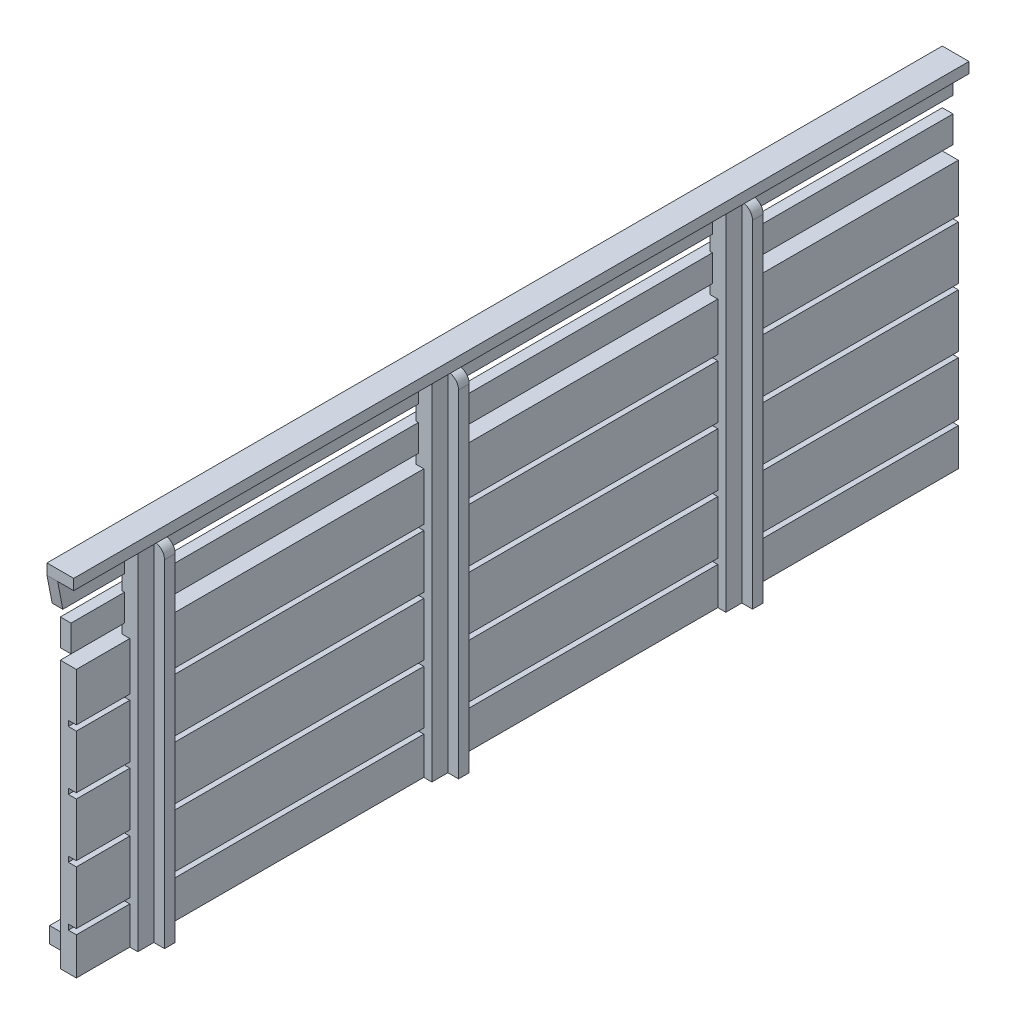
SolidWorks part; units mm, degrees
ref_plane "Front Plane" through (0, 0, 0) normal (0, 0, 1) x (1, 0, 0)
ref_plane "Top Plane" through (0, 0, 0) normal (0, 1, 0) x (1, 0, 0)
ref_plane "Right Plane" through (0, 0, 0) normal (1, 0, 0) x (0, 0, -1)
sketch "Sketch1" plane through (0, 0, 0) normal (1, 0, 0) x (0, 0, -1)
  line L1 (-82.5, 25) -> (82.5, 25)
  line L2 (-82.5, 25) -> (-82.5, -25)
  line L3 (-82.5, -25) -> (82.5, -25)
  line L4 (82.5, 25) -> (82.5, -25)
  line L5 (-82.5, 25) -> (82.5, -25) construction
  line L6 (-82.5, -25) -> (82.5, 25) construction
  point P0 (0, 0)
  dimension "D1" = 165
  dimension "D2" = 50
extrude "Boss-Extrude1" add sketch "Sketch1" along normal blind 3
sketch "Sketch2" plane through (3, 0, 0) normal (1, 0, 0) x (0, 0, -1)
  line L0 (-82.5, 25) -> (-82.5, -25) construction
  line L1 (-82.5, -17) -> (82.5, -17)
  line L2 (-82.5, -17) -> (-82.5, -18)
  line L3 (-82.5, -18) -> (82.5, -18)
  line L4 (82.5, -17) -> (82.5, -18)
  line L5 (82.5, -25) -> (82.5, 25) construction
  line L6 (-82.5, -25) -> (82.5, -25) construction
  line L7 (82.5, 25) -> (-82.5, 25) construction
  line L8 (-82.5, -6) -> (82.5, -6)
  line L9 (-82.5, -6) -> (-82.5, -7)
  line L10 (-82.5, -7) -> (82.5, -7)
  line L11 (82.5, -6) -> (82.5, -7)
  line L12 (-82.5, 5) -> (82.5, 5)
  line L13 (-82.5, 5) -> (-82.5, 4)
  line L14 (-82.5, 4) -> (82.5, 4)
  line L15 (82.5, 5) -> (82.5, 4)
  line L16 (-82.5, 16) -> (82.5, 16)
  line L17 (-82.5, 16) -> (-82.5, 15)
  line L18 (-82.5, 15) -> (82.5, 15)
  line L19 (82.5, 16) -> (82.5, 15)
  dimension "D1" = 1
  dimension "D2" = 7
  dimension "D3" = 1
  dimension "D4" = 10
  dimension "D5" = 1
  dimension "D6" = 10
  dimension "D7" = 1
  dimension "D8" = 10
  dimension "D9" = 9
extrude "Cut-Extrude1" cut sketch "Sketch2" against normal blind 1.5
sketch "Sketch3" plane through (3, 0, 0) normal (1, 0, 0) x (0, 0, -1)
  line L6 (-67.5, -25) -> (-72.5, -25)
  line L7 (-82.5, -25) -> (82.5, -25) construction
  line L8 (42.5, -25) -> (37.5, -25)
  line L9 (42.5, -25) -> (42.5, 40)
  line L10 (42.5, 40) -> (37.5, 40)
  line L11 (37.5, -25) -> (37.5, 40)
  line L12 (82.5, -25) -> (82.5, -18) construction
  line L13 (-67.5, -25) -> (-67.5, 40)
  line L14 (-12.5, -25) -> (-17.5, -25)
  line L15 (-12.5, -25) -> (-12.5, 40)
  line L16 (-12.5, 40) -> (-17.5, 40)
  line L17 (-17.5, -25) -> (-17.5, 40)
  line L22 (-67.5, 40) -> (-72.5, 40)
  line L23 (-72.5, -25) -> (-72.5, 40)
  dimension "D1" = 65
  dimension "D2" = 40
  dimension "D3" = 5
  dimension "D4" = 5
  dimension "D5" = 65
  dimension "D6" = 50
  dimension "D7" = 5
  dimension "D8" = 50
  dimension "D9" = 65
extrude "Boss-Extrude2" add sketch "Sketch3" along normal mid plane 3
sketch "Sketch4" plane through (4.5, 0, 0) normal (1, 0, 0) x (0, 0, -1)
  line L0 (42.5, 40) -> (37.5, 40) construction
  line L1 (42.5, -25) -> (40.5, -25)
  line L2 (42.5, -25) -> (42.5, 40)
  line L3 (42.5, 40) -> (40.5, 40)
  line L4 (40.5, -25) -> (40.5, 40)
  line L5 (-12.5, 40) -> (-17.5, 40) construction
  line L6 (-12.5, -25) -> (-14.5, -25)
  line L7 (-12.5, -25) -> (-12.5, 40)
  line L8 (-12.5, 40) -> (-14.5, 40)
  line L9 (-14.5, -25) -> (-14.5, 40)
  line L16 (-67.5, 40) -> (-72.5, 40) construction
  line L17 (-67.5, -25) -> (-69.5, -25)
  line L18 (-67.5, -25) -> (-67.5, 40)
  line L19 (-67.5, 40) -> (-69.5, 40)
  line L20 (-69.5, -25) -> (-69.5, 40)
  dimension "D1" = 2
  dimension "D2" = 2
  dimension "D3" = 2
extrude "Boss-Extrude3" add sketch "Sketch4" along normal blind 2
fillet "Fillet1" radius 2 3 edges at (6.5, 40, 68.5) (6.5, 40, 13.5) (6.5, 40, -41.5)
sketch "Sketch5" plane through (0, 0, 0) normal (-1, 0, 0) x (0, 0, 1)
  line L5 (82.5, -25) -> (82.5, 70.4394) construction
  line L10 (-82.5, -25) -> (-82.5, 70.4394) construction
  line L15 (-82.5, 25) -> (82.5, 25) construction
  line L16 (-82.5, 27) -> (82.5, 27)
  line L17 (-82.5, 27) -> (-82.5, 32)
  line L18 (-82.5, 32) -> (82.5, 32)
  line L19 (82.5, 27) -> (82.5, 32)
  line L21 (-82.5, 40) -> (85, 40)
  line L22 (-82.5, 40) -> (-82.5, 35)
  line L23 (-82.5, 35) -> (85, 35)
  line L24 (85, 40) -> (85, 35)
  dimension "D1" = 165
  dimension "D2" = 2
  dimension "D3" = 5
  dimension "D4" = 5
  dimension "D5" = 3
extrude "Boss-Extrude4" add sketch "Sketch5" against normal blind 2 separate body
sketch "Sketch7" plane through (0, 0, 0) normal (-1, 0, 0) x (0, 0, 1)
  line L0 (82.5, 25) -> (82.5, -25) construction
  line L1 (-82.5, -25) -> (82.5, -25)
  line L2 (-82.5, -25) -> (-82.5, -22)
  line L3 (-82.5, -22) -> (82.5, -22)
  line L4 (82.5, -25) -> (82.5, -22)
  dimension "D1" = 3
extrude "Boss-Extrude5" add sketch "Sketch7" along normal blind 5
sketch "Sketch8" plane through (0, 40, 0) normal (0, 1, 0) x (1, 0, 0)
  line L1 (0, 82.5) -> (5, 82.5)
  line L2 (0, 82.5) -> (0, -84.9948)
  line L3 (0, -84.9948) -> (5, -84.9948)
  line L4 (5, 82.5) -> (5, -84.9948)
  dimension "D1" = 5
  dimension "D2" = 167.4948
extrude "Boss-Extrude6" add sketch "Sketch8" along normal blind 2
sketch "Sketch12" plane through (0, -22, 0) normal (0, 1, 0) x (1, 0, 0)
  line L0 (-5, -82.5) -> (-5, 82.5) construction
  line L1 (0, -82.5) -> (-5, -82.5)
  line L2 (0, -82.5) -> (0, -79.5)
  line L3 (0, -79.5) -> (-5, -79.5)
  line L4 (-5, -82.5) -> (-5, -79.5)
  dimension "D1" = 3
extrude "Cut-Extrude3" cut sketch "Sketch12" against normal up to surface (3 mm away) up to face at (3.6364, -25, 12.1364)
sketch "Sketch13" plane through (2, 0, 0) normal (1, 0, 0) x (0, 0, -1)
  line L3 (-82.5, 27) -> (-84.9948, 40)
  line L4 (-84.9948, 40) -> (-86.3567, 40)
  line L5 (-86.3567, 40) -> (-86.3567, 27)
  line L6 (-86.3567, 27) -> (-82.5, 27)
extrude "Cut-Extrude5" cut sketch "Sketch13" against normal blind 10
sketch "Sketch10" plane through (0, 0, 84.9948) normal (0, 0, 1) x (1, 0, 0)
  line L4 (2, 42) -> (2, 40)
  line L5 (2, 40) -> (5, 40)
  line L6 (5, 40) -> (5, 42)
  line L7 (5, 42) -> (2, 42)
  line L8 (2, 42) -> (2, 40)
  line L9 (2, 40) -> (5, 40)
  line L10 (5, 40) -> (5, 42)
  line L11 (5, 42) -> (2, 42)
  dimension "D1" = 0
